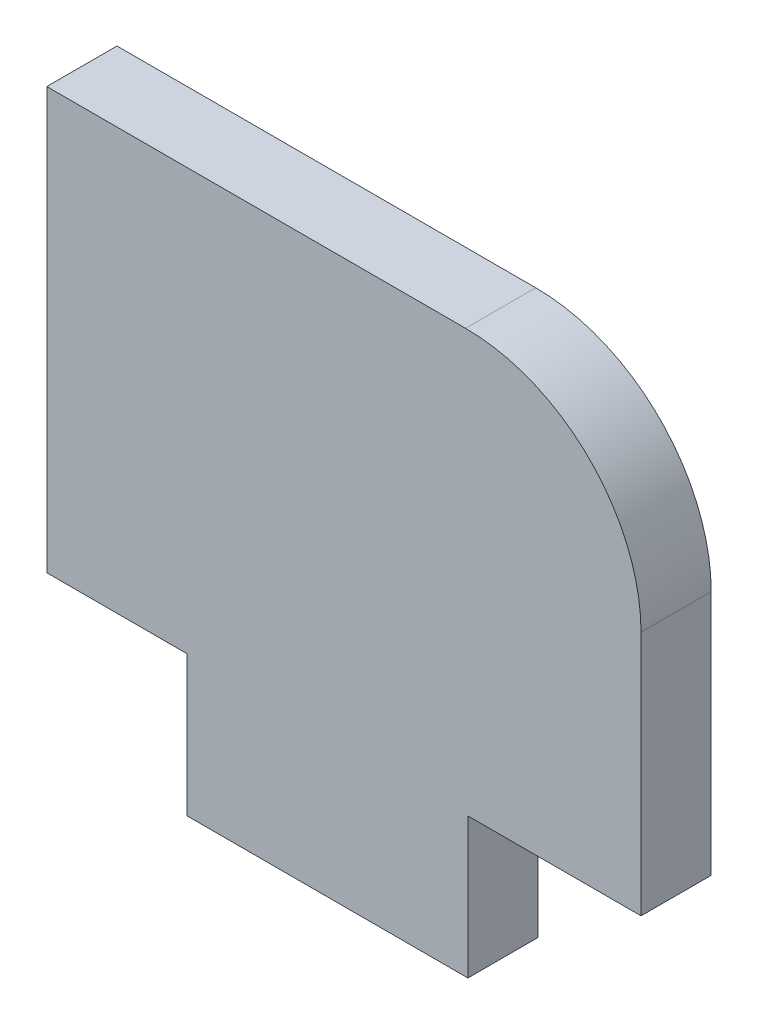
SolidWorks part; units mm, degrees
ref_plane "Front Plane" through (0, 0, 0) normal (0, 0, 1) x (1, 0, 0)
ref_plane "Top Plane" through (0, 0, 0) normal (0, 1, 0) x (1, 0, 0)
ref_plane "Right Plane" through (0, 0, 0) normal (1, 0, 0) x (0, 0, -1)
sketch "Sketch1" plane through (0, 0, 0) normal (0, 0, 1) x (1, 0, 0)
  line L0 (5.5334, -4) -> (10.4666, -4)
  line L1 (-2.4666, -4) -> (-6.4666, -4)
  line L2 (-6.4666, -4) -> (-6.4666, 8)
  line L3 (-6.4666, 8) -> (5.4666, 8)
  line L4 (5.5334, -4) -> (5.5334, -8)
  line L5 (5.5334, -8) -> (-2.4666, -8)
  line L6 (-2.4666, -8) -> (-2.4666, -4)
  line L7 (10.4666, 3) -> (10.4666, -4)
  arc A0 (10.4666, 3) -> (5.4666, 8) centre (5.4666, 3) ccw
  dimension "D1" = 5
  dimension "D2" = 5.5334
  dimension "D3" = 10.4666
  dimension "D4" = 2.4666
  dimension "D5" = 6.4666
  dimension "D6" = 8
  dimension "D7" = 4
extrude "Boss-Extrude1" add sketch "Sketch1" along normal blind 2
